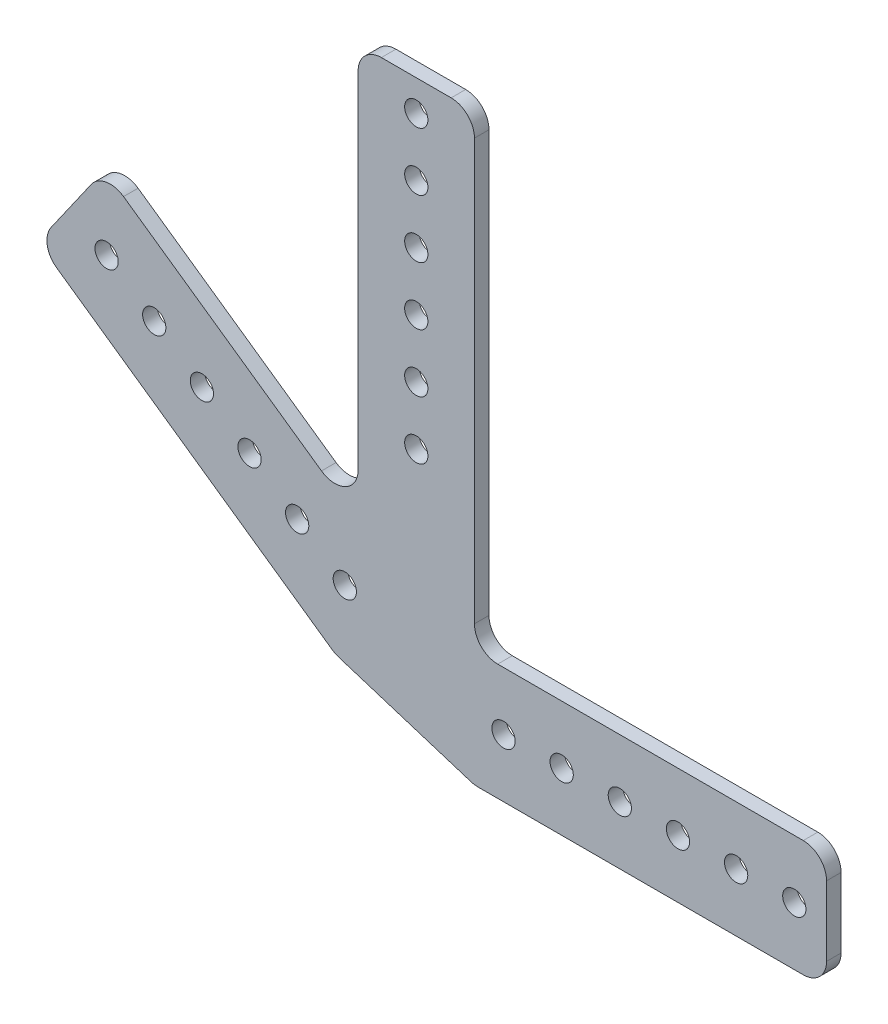
SolidWorks part; units mm, degrees
ref_plane "Front Plane" through (0, 0, 0) normal (0, 0, 1) x (1, 0, 0)
ref_plane "Top Plane" through (0, 0, 0) normal (0, 1, 0) x (1, 0, 0)
ref_plane "Right Plane" through (0, 0, 0) normal (1, 0, 0) x (0, 0, -1)
sketch "Sketch1" plane through (0, 0, 0) normal (0, 0, 1) x (1, 0, 0)
  line L0 (-280.0652, 184.4073) -> (-30.3877, 9.5812)
  line L1 (0, 0) -> (431.8, 0)
  line L2 (0, 0) -> (0, 25.4)
  line L3 (0, 25.4) -> (431.8, 25.4)
  line L4 (431.8, 0) -> (431.8, 25.4)
  line L5 (-280.0652, 184.4073) -> (-265.4964, 205.2137)
  line L6 (-30.3877, 9.5812) -> (-15.8188, 30.3877)
  line L7 (-265.4964, 205.2137) -> (-15.8188, 30.3877)
  line L8 (-25.4, 50.8) -> (0, 50.8)
  line L9 (-25.4, 50.8) -> (-25.4, 355.6)
  line L10 (0, 50.8) -> (0, 355.6)
  line L11 (-25.4, 355.6) -> (0, 355.6)
  line L12 (-225.8432, 161.9445) -> (23.8343, -12.8816) construction
  line L13 (0, 12.7) -> (431.8, 12.7) construction
  line L14 (-12.7, 12.7) -> (-12.7, 105.3379) construction
  line L15 (-12.7, 57.15) -> (-12.7, 69.85) construction
  line L16 (6.35, 12.7) -> (19.05, 12.7) construction
  line L17 (-28.3048, 23.6266) -> (-38.7081, 30.9111) construction
  circle A0 centre (-12.7, 57.15) radius 2.54
  circle A1 centre (-12.7, 69.85) radius 2.54
  circle A2 centre (-12.7, 82.55) radius 2.54
  circle A3 centre (-12.7, 95.25) radius 2.54
  circle A4 centre (-12.7, 107.95) radius 2.54
  circle A5 centre (-12.7, 120.65) radius 2.54
  circle A6 centre (-12.7, 133.35) radius 2.54
  circle A7 centre (-12.7, 146.05) radius 2.54
  circle A8 centre (-12.7, 158.75) radius 2.54
  circle A9 centre (-12.7, 171.45) radius 2.54
  circle A10 centre (-12.7, 184.15) radius 2.54
  circle A11 centre (-12.7, 196.85) radius 2.54
  circle A12 centre (-12.7, 209.55) radius 2.54
  circle A13 centre (-12.7, 222.25) radius 2.54
  circle A14 centre (-12.7, 234.95) radius 2.54
  circle A15 centre (-12.7, 247.65) radius 2.54
  circle A16 centre (-12.7, 260.35) radius 2.54
  circle A17 centre (-12.7, 273.05) radius 2.54
  circle A18 centre (-12.7, 285.75) radius 2.54
  circle A19 centre (-12.7, 298.45) radius 2.54
  circle A20 centre (-12.7, 311.15) radius 2.54
  circle A21 centre (-12.7, 323.85) radius 2.54
  circle A22 centre (-12.7, 336.55) radius 2.54
  circle A23 centre (-12.7, 349.25) radius 2.54
  circle A24 centre (6.35, 12.7) radius 2.54
  circle A25 centre (19.05, 12.7) radius 2.54
  circle A26 centre (31.75, 12.7) radius 2.54
  circle A27 centre (44.45, 12.7) radius 2.54
  circle A28 centre (57.15, 12.7) radius 2.54
  circle A29 centre (69.85, 12.7) radius 2.54
  circle A30 centre (82.55, 12.7) radius 2.54
  circle A31 centre (95.25, 12.7) radius 2.54
  circle A32 centre (107.95, 12.7) radius 2.54
  circle A33 centre (120.65, 12.7) radius 2.54
  circle A34 centre (133.35, 12.7) radius 2.54
  circle A35 centre (146.05, 12.7) radius 2.54
  circle A36 centre (158.75, 12.7) radius 2.54
  circle A37 centre (171.45, 12.7) radius 2.54
  circle A38 centre (184.15, 12.7) radius 2.54
  circle A39 centre (196.85, 12.7) radius 2.54
  circle A40 centre (209.55, 12.7) radius 2.54
  circle A41 centre (222.25, 12.7) radius 2.54
  circle A42 centre (234.95, 12.7) radius 2.54
  circle A43 centre (247.65, 12.7) radius 2.54
  circle A44 centre (260.35, 12.7) radius 2.54
  circle A45 centre (273.05, 12.7) radius 2.54
  circle A46 centre (285.75, 12.7) radius 2.54
  circle A47 centre (298.45, 12.7) radius 2.54
  circle A48 centre (311.15, 12.7) radius 2.54
  circle A49 centre (323.85, 12.7) radius 2.54
  circle A50 centre (336.55, 12.7) radius 2.54
  circle A51 centre (349.25, 12.7) radius 2.54
  circle A52 centre (361.95, 12.7) radius 2.54
  circle A53 centre (374.65, 12.7) radius 2.54
  circle A54 centre (387.35, 12.7) radius 2.54
  circle A55 centre (400.05, 12.7) radius 2.54
  circle A56 centre (412.75, 12.7) radius 2.54
  circle A57 centre (425.45, 12.7) radius 2.54
  circle A58 centre (-28.3048, 23.6266) radius 2.54
  circle A59 centre (-38.7081, 30.9111) radius 2.54
  circle A60 centre (-49.1113, 38.1955) radius 2.54
  circle A61 centre (-59.5145, 45.4799) radius 2.54
  circle A62 centre (-69.9178, 52.7643) radius 2.54
  circle A63 centre (-80.321, 60.0487) radius 2.54
  circle A64 centre (-90.7242, 67.3332) radius 2.54
  circle A65 centre (-101.1275, 74.6176) radius 2.54
  circle A66 centre (-111.5307, 81.902) radius 2.54
  circle A67 centre (-121.9339, 89.1864) radius 2.54
  circle A68 centre (-132.3372, 96.4708) radius 2.54
  circle A69 centre (-142.7404, 103.7553) radius 2.54
  circle A70 centre (-153.1436, 111.0397) radius 2.54
  circle A71 centre (-163.5468, 118.3241) radius 2.54
  circle A72 centre (-173.9501, 125.6085) radius 2.54
  circle A73 centre (-184.3533, 132.8929) radius 2.54
  circle A74 centre (-194.7565, 140.1774) radius 2.54
  circle A75 centre (-205.1598, 147.4618) radius 2.54
  circle A76 centre (-215.563, 154.7462) radius 2.54
  circle A77 centre (-225.9662, 162.0306) radius 2.54
  circle A78 centre (-236.3695, 169.315) radius 2.54
  circle A79 centre (-246.7727, 176.5995) radius 2.54
  circle A80 centre (-257.1759, 183.8839) radius 2.54
  circle A81 centre (-267.5792, 191.1683) radius 2.54
  point P12 (-23.1032, 19.9844)
  point P17 (0, 12.7)
  point P19 (-12.7, 12.7)
  point P22 (-12.7, 50.8)
  dimension "D12" = 5.08
  dimension "D15" = 5.08
  dimension "D19" = 5.08
  dimension "D20" = 6.35
  dimension "D1" = 25.4
  dimension "D2" = 431.8
  dimension "D3" = 25.4
  dimension "D4" = 25.4
  dimension "D5" = 304.8
  dimension "D6" = 304.8
  dimension "D7" = 145
  dimension "D8" = 12.7
  dimension "D9" = 12.7
  dimension "D10" = 38.1
  dimension "D11" = 6.35
  dimension "D14" = 12.7
  dimension "D16" = 6.35
  dimension "D18" = 12.7
  dimension "D21" = 12.7
  dimension "D13" = 24
  dimension "D17" = 34
ref_plane "Plane1" through (0, 0, 0) normal (0, 0, 1) x (1, 0, 0)
sketch "Sketch2" plane through (0, 0, 0) normal (0, 0, 1) x (1, 0, 0)
  line L0 (-20.32, 127.4043) -> (-5.08, 127.4043)
  line L1 (-25.4, 50.8) -> (-25.4, 355.6) construction
  line L2 (0, 50.8) -> (0, 355.6) construction
  line L3 (0, 122.3243) -> (0, 50.8)
  line L4 (0, 50.8) -> (0, 30.48)
  line L5 (5.08, 25.4) -> (71.8116, 25.4)
  line L6 (0, 25.4) -> (431.8, 25.4) construction
  line L7 (76.8916, 20.32) -> (76.8916, 5.08)
  line L8 (0, 0) -> (431.8, 0) construction
  line L9 (71.8116, 0) -> (0.7819, 0)
  line L10 (-0.7457, 0.2351) -> (-29.642, 9.3461)
  line L11 (-31.0281, 10.0297) -> (-91.19, 52.1554)
  line L12 (-280.0652, 184.4073) -> (-30.3877, 9.5812) construction
  line L13 (-92.4375, 59.2305) -> (-83.6962, 71.7144)
  line L14 (-265.4964, 205.2137) -> (-15.8188, 30.3877) construction
  line L15 (-76.6211, 72.9619) -> (-33.3938, 42.6938)
  line L16 (-25.4, 46.8551) -> (-25.4, 122.3243)
  arc A0 (71.8116, 25.4) -> (76.8916, 20.32) centre (71.8116, 20.32) cw
  arc A1 (76.8916, 5.08) -> (71.8116, 0) centre (71.8116, 5.08) cw
  arc A2 (0.7819, 0) -> (-0.7457, 0.2351) centre (0.7819, 5.08) cw
  arc A3 (-29.642, 9.3461) -> (-31.0281, 10.0297) centre (-28.1144, 14.191) cw
  arc A4 (-91.19, 52.1554) -> (-92.4375, 59.2305) centre (-88.2762, 56.3167) cw
  arc A5 (-83.6962, 71.7144) -> (-76.6211, 72.9619) centre (-79.5349, 68.8006) cw
  arc A6 (-33.3938, 42.6938) -> (-25.4, 46.8551) centre (-30.48, 46.8551) ccw
  arc A7 (0, 30.48) -> (5.08, 25.4) centre (5.08, 30.48) ccw
  arc A8 (-5.08, 127.4043) -> (0, 122.3243) centre (-5.08, 122.3243) cw
  arc A9 (-20.32, 127.4043) -> (-25.4, 122.3243) centre (-20.32, 122.3243) ccw
  point P29 (76.8916, 25.4)
  point P32 (76.8916, 0)
  point P35 (0, 0)
  point P38 (-30.3877, 9.5812)
  point P41 (-95.3513, 55.0692)
  point P44 (-80.7824, 75.8757)
  point P47 (-25.4, 37.0965)
  point P50 (0, 25.4)
  point P53 (0, 127.4043)
  point P56 (-25.4, 127.4043)
  dimension "D1" = 5.08
extrude "Boss-Extrude1" add sketch "Sketch2" along normal blind 3.175
sketch "Sketch3" plane through (0, 0, 0) normal (0, 0, 1) x (1, 0, 0)
  circle A0 centre (-12.7, 57.15) radius 2.54
  circle A1 centre (6.35, 12.7) radius 2.54
  circle A2 centre (-28.3048, 23.6266) radius 2.54
  circle A3 centre (-38.7081, 30.9111) radius 2.54
  circle A4 centre (-49.1113, 38.1955) radius 2.54
  circle A5 centre (-59.5145, 45.4799) radius 2.54
  circle A6 centre (-69.9178, 52.7643) radius 2.54
  circle A7 centre (-80.321, 60.0487) radius 2.54
  circle A8 centre (-12.7, 69.85) radius 2.54
  circle A9 centre (-12.7, 82.55) radius 2.54
  circle A10 centre (-12.7, 95.25) radius 2.54
  circle A11 centre (-12.7, 107.95) radius 2.54
  circle A12 centre (-12.7, 120.65) radius 2.54
  circle A13 centre (19.05, 12.7) radius 2.54
  circle A14 centre (31.75, 12.7) radius 2.54
  circle A15 centre (44.45, 12.7) radius 2.54
  circle A16 centre (57.15, 12.7) radius 2.54
  circle A17 centre (69.85, 12.7) radius 2.54
  dimension "D1" = 6
  dimension "D2" = 6
  dimension "D3" = 6
extrude "Cut-Extrude5" cut sketch "Sketch3" against normal through all both and the other way through all from surface at 3.175 starting at face at (-10.5565, 48.5541, 3.175)
